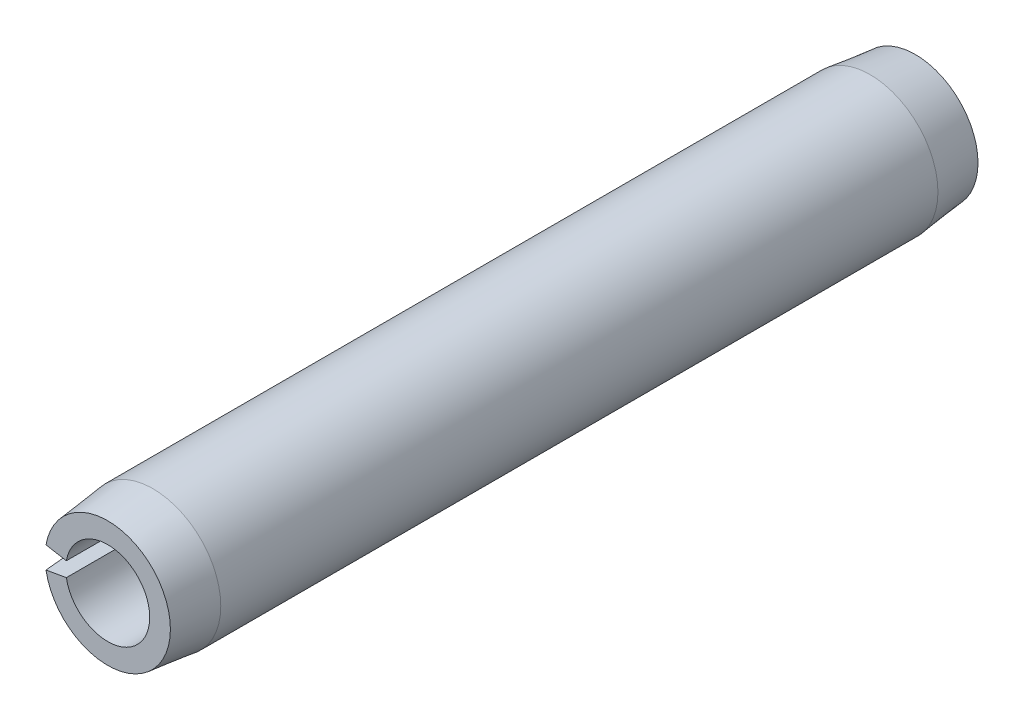
SolidWorks part; units mm, degrees
ref_plane "Front Plane" through (0, 0, 0) normal (0, 0, 1) x (1, 0, 0)
ref_plane "Top Plane" through (0, 0, 0) normal (0, 1, 0) x (1, 0, 0)
ref_plane "Right Plane" through (0, 0, 0) normal (1, 0, 0) x (0, 0, -1)
sketch "Sketch5" plane through (0, 0, 0) normal (0, 0, 1) x (1, 0, 0)
  line L0 (0.4953, 0) -> (0.8001, 0) construction
  line L1 (-0.7879, 0.1389) -> (-0.4878, 0.086)
  line L2 (-0.4878, -0.086) -> (-0.7879, -0.1389)
  arc A0 (-0.7879, -0.1389) -> (-0.7879, 0.1389) centre (0, 0) ccw
  arc A1 (-0.4878, -0.086) -> (-0.4878, 0.086) centre (0, 0) ccw
  circle A2 centre (0, 0) radius 0.8001 construction
  dimension "Diameter" = 1.6002
  dimension "Wall Thickness" = 0.3048
  dimension "Opening Angle" = 20
sketch "Sketch6" plane through (0, 0, 0) normal (1, 0, 0) x (0, 0, -1)
  line L0 (4.7625, 0) -> (-4.7625, 0) construction
  line L1 (0, 0.8001) -> (0, -0.8001) construction
  line L4 (0, 0.8001) -> (0, -0.8001) construction
  line L5 (4.7625, 0) -> (4.7625, 0.8001) construction
  line L6 (4.7625, 0.8001) -> (-4.7625, 0.8001) construction
  line L7 (-4.7625, 0.8001) -> (-4.7625, 0) construction
  line L8 (4.7625, 0.7391) -> (4.2291, 0.8001)
  dimension "Length" = 9.525
  dimension "Chamfer" = 0.5334
  dimension "D1" = 0.061
sketch "Sketch1" plane through (0, 0, 0) normal (0, 0, 1) x (1, 0, 0)
  line L1 (-0.4878, -0.086) -> (-0.7879, -0.1389) construction
  line L2 (-0.7879, 0.1389) -> (-0.4878, 0.086) construction
  line L3 (-0.4878, -0.086) -> (-0.7879, -0.1389)
  line L4 (-0.7879, 0.1389) -> (-0.4878, 0.086)
  arc A2 (-0.7879, -0.1389) -> (-0.7879, 0.1389) centre (0, 0) ccw construction
  arc A3 (-0.4878, -0.086) -> (-0.4878, 0.086) centre (0, 0) ccw construction
  arc A4 (-0.7879, -0.1389) -> (-0.7879, 0.1389) centre (0, 0) ccw
  arc A5 (-0.4878, -0.086) -> (-0.4878, 0.086) centre (0, 0) ccw
extrude "Extrude1" add sketch "Sketch1" against normal up to vertex (4.7625 mm away) and the other way up to vertex (4.7625 mm away) up to point (0, 0.8001, -4.7625) other way up to point (0, 0.8001, 4.7625)
sketch "Sketch2" plane through (0, 0, 0) normal (1, 0, 0) x (0, 0, -1)
  line L0 (4.7625, 0.7391) -> (4.2291, 0.8001)
  line L1 (4.2291, 0.8001) -> (4.7625, 0.8001)
  line L4 (4.7625, 0.8001) -> (4.7625, 0.7391)
revolve "Cut-Revolve1" cut sketch "Sketch2" angle 360 about L0
mirror "Mirror1" about plane through (0, 0, 0) normal (0, 0, 1) of "Cut-Revolve1"
equation "\"D1@Sketch6\"=\"Wall Thickness@Sketch5\"*.2"
equation "\"Chamfer@Sketch6\"=\"Diameter@Sketch5\"/3"
